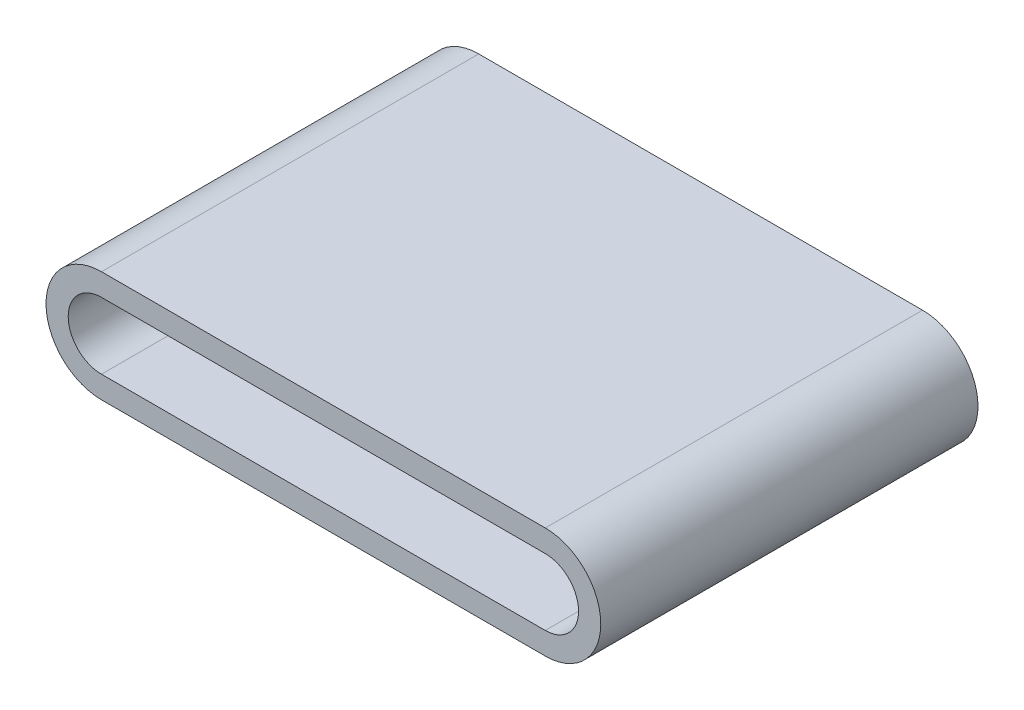
SolidWorks part; units mm, degrees
ref_plane "前视基准面" through (0, 0, 0) normal (0, 0, 1) x (1, 0, 0)
ref_plane "上视基准面" through (0, 0, 0) normal (0, 1, 0) x (1, 0, 0)
ref_plane "右视基准面" through (0, 0, 0) normal (1, 0, 0) x (0, 0, -1)
sketch "草图3" plane through (0, 0, 0) normal (0, 0, 1) x (1, 0, 0)
  line L0 (0, 0) -> (100, 0) construction
  line L1 (0, 12.5) -> (100, 12.5)
  line L2 (0, -12.5) -> (100, -12.5)
  arc A0 (0, 12.5) -> (0, -12.5) centre (0, 0) ccw
  arc A1 (100, -12.5) -> (100, 12.5) centre (100, 0) ccw
  point P3 (50, 0)
  dimension "D1" = 100
  dimension "D2" = 25
extrude "凸台-拉伸2" add sketch "草图3" along normal blind 20 and the other way blind 10
sketch "草图4" plane through (0, 0, 20) normal (0, 0, 1) x (1, 0, 0)
  line L2 (0, -12.5) -> (100, -12.5)
  line L3 (100, 12.5) -> (0, 12.5)
  line L4 (0, -12.5) -> (100, -12.5)
  line L5 (100, 12.5) -> (0, 12.5)
  arc A2 (0, 12.5) -> (0, -12.5) centre (0, 0) ccw
  arc A3 (100, -12.5) -> (100, 12.5) centre (100, 0) ccw
  arc A4 (0, 12.5) -> (0, -12.5) centre (0, 0) ccw
  arc A5 (100, -12.5) -> (100, 12.5) centre (100, 0) ccw
  dimension "D1" = 0
extrude "拉伸-薄壁1" add sketch "草图4" along normal blind 55 thin thin type one direction reverse wall 5
